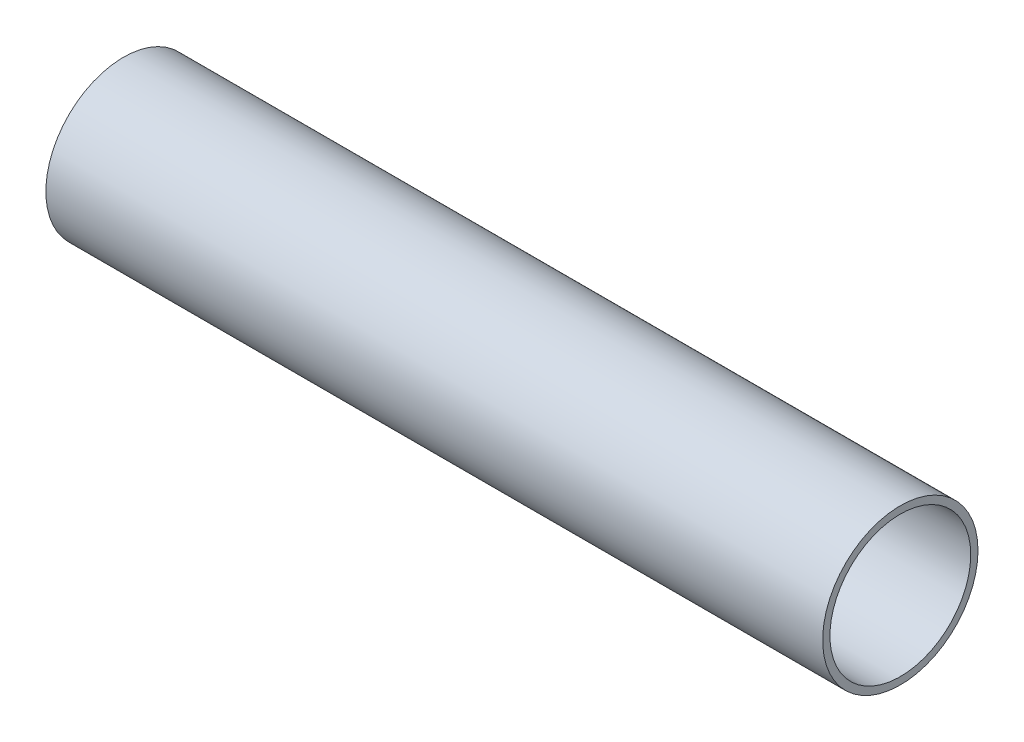
SolidWorks part; units mm, degrees
material "2024 Alloy"
ref_plane "Front Plane" through (0, 0, 0) normal (0, 0, 1) x (1, 0, 0)
ref_plane "Top Plane" through (0, 0, 0) normal (0, 1, 0) x (1, 0, 0)
ref_plane "Right Plane" through (0, 0, 0) normal (1, 0, 0) x (0, 0, -1)
sketch "Sketch1" plane through (0, 0, 0) normal (0, 0, 1) x (1, 0, 0)
  line L0 (0, 8) -> (0, 7.25)
  line L1 (0, 7.25) -> (80, 7.25)
  line L2 (80, 7.25) -> (80, 8)
  line L3 (80, 8) -> (0, 8)
  line L4 (0, 0) -> (80, 0) construction
revolve "Revolve1" add sketch "Sketch1" angle 360 about L4
